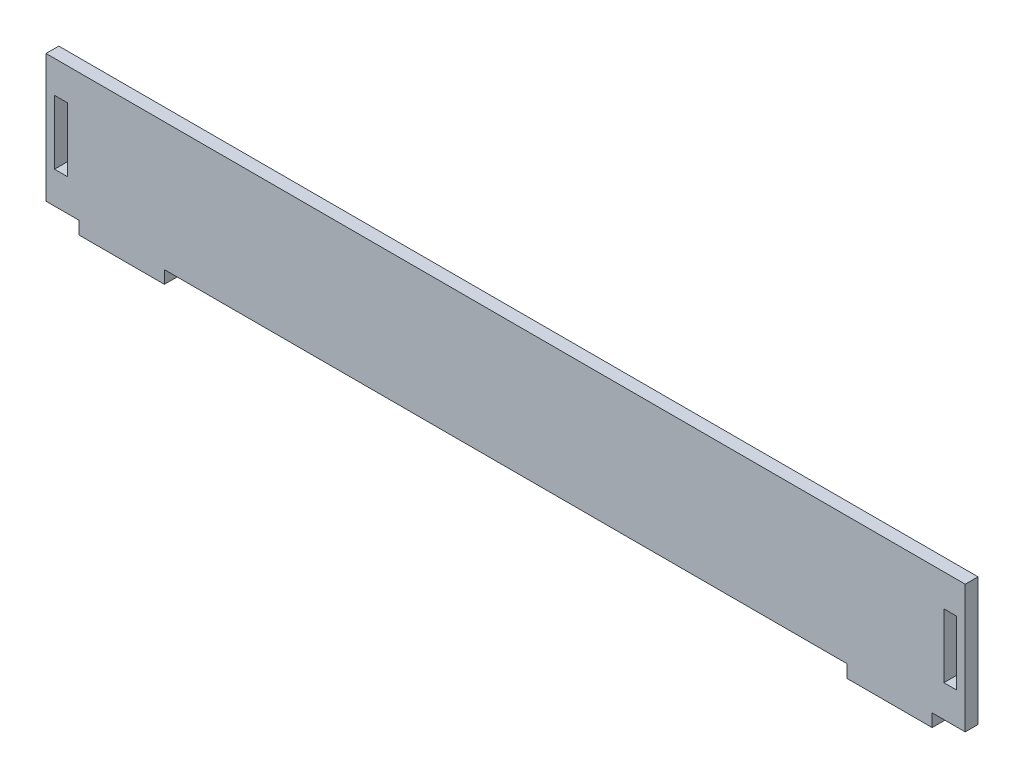
SolidWorks part; units mm, degrees
ref_plane "前视基准面" through (0, 0, 0) normal (0, 0, 1) x (1, 0, 0)
ref_plane "上视基准面" through (0, 0, 0) normal (0, 1, 0) x (1, 0, 0)
ref_plane "右视基准面" through (0, 0, 0) normal (1, 0, 0) x (0, 0, -1)
sketch "草图1" plane through (0, 0, 0) normal (0, 0, 1) x (1, 0, 0)
  line L0 (202.75, 15) -> (202.75, 22.5)
  line L1 (0, 0) -> (200, 0)
  line L3 (0, 30) -> (200, 30)
  line L5 (0, 0) -> (20, 0)
  line L6 (0, 0) -> (0, -3)
  line L7 (0, -3) -> (20, -3)
  line L8 (20, 0) -> (20, -3)
  line L9 (200, 0) -> (180, 0)
  line L10 (200, 0) -> (200, -3)
  line L11 (200, -3) -> (180, -3)
  line L12 (180, 0) -> (180, -3)
  line L13 (200, 30) -> (202.75, 30)
  line L15 (200, 0) -> (202.75, 0)
  line L16 (202.75, 22.5) -> (202.75, 7.5)
  line L17 (202.75, 30) -> (207.75, 30)
  line L18 (202.75, 22.5) -> (202.75, 7.5)
  line L19 (202.75, 0) -> (207.75, 0)
  line L20 (207.75, 30) -> (207.75, 0)
  line L21 (202.75, 22.5) -> (205.75, 22.5)
  line L22 (205.75, 22.5) -> (205.75, 7.5)
  line L23 (205.75, 7.5) -> (202.75, 7.5)
  line L24 (-2.75, 15) -> (-2.75, 22.5)
  line L25 (0, 30) -> (-2.75, 30)
  line L27 (0, 0) -> (-2.75, 0)
  line L28 (-2.75, 22.5) -> (-2.75, 7.5)
  line L29 (-2.75, 30) -> (-7.75, 30)
  line L30 (-2.75, 22.5) -> (-2.75, 7.5)
  line L31 (-2.75, 0) -> (-7.75, 0)
  line L32 (-7.75, 30) -> (-7.75, 0)
  line L33 (-2.75, 22.5) -> (-5.75, 22.5)
  line L34 (-5.75, 22.5) -> (-5.75, 7.5)
  line L35 (-5.75, 7.5) -> (-2.75, 7.5)
extrude "凸台-拉伸1" add sketch "草图1" along normal blind 3 contours L29 L32 L31 L27 L1 L15 L19 L20 L17 L13 L3 L25 L35 L34 L33 L24 L28 L22 L23 L16 L0 L21 | L8 L1 L6 L7 | L10 L11 L12 L9
